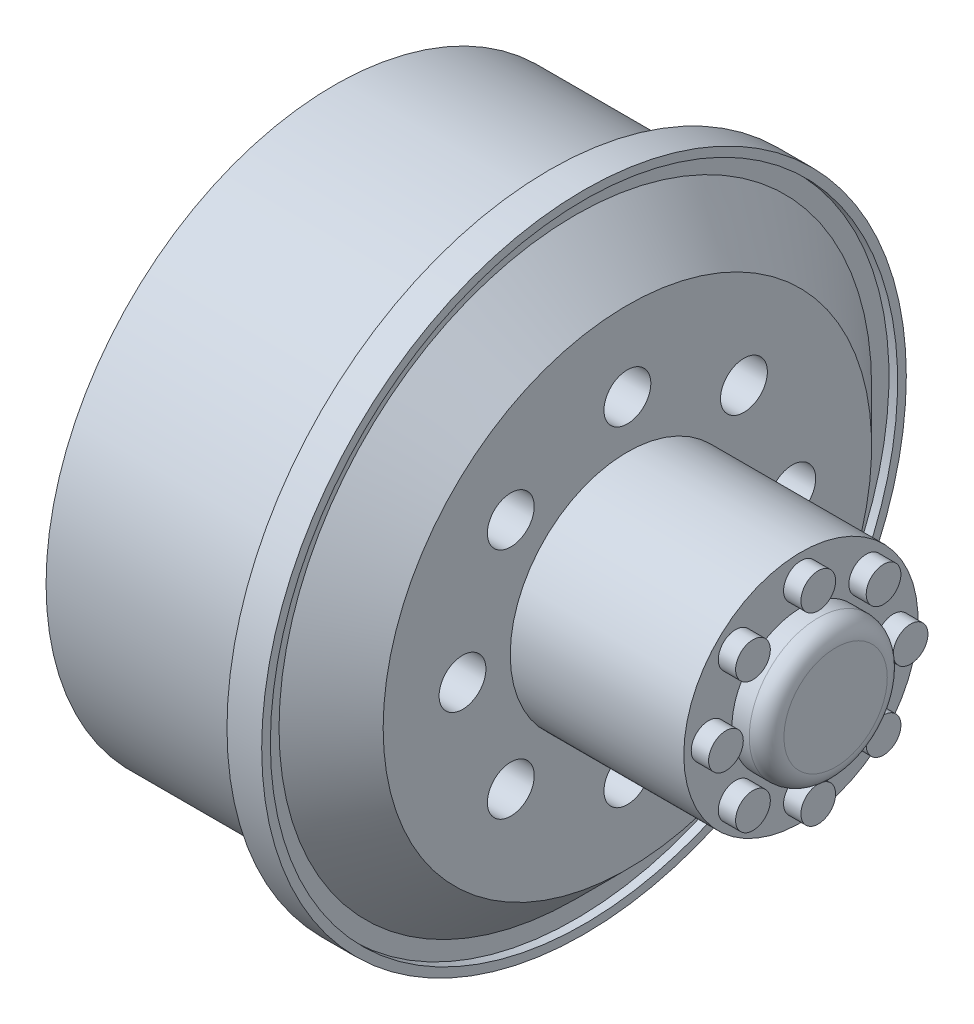
SolidWorks part; units mm, degrees
ref_plane "Front Plane" through (0, 0, 0) normal (0, 0, 1) x (1, 0, 0)
ref_plane "Top Plane" through (0, 0, 0) normal (0, 1, 0) x (1, 0, 0)
ref_plane "Right Plane" through (0, 0, 0) normal (1, 0, 0) x (0, 0, -1)
sketch "Sketch1" plane through (0, 0, 0) normal (0, 0, 1) x (1, 0, 0)
  line L0 (-25, 0) -> (25, 0) construction
  line L1 (0, 58.2583) -> (0, -54.955) construction
  line L2 (-9.3086, 16.6) -> (3.0914, 16.6)
  line L3 (3.0914, 16.6) -> (3.0914, 18.5746)
  line L4 (3.0914, 18.5746) -> (5.0914, 18.5746)
  line L5 (5.0914, 18.5746) -> (5.0914, 18.0746)
  line L6 (5.0914, 18.0746) -> (4.5914, 18.0746)
  line L7 (4.5914, 18.0746) -> (4.5914, 17.0746)
  line L8 (4.5914, 17.0746) -> (7.5914, 14.0746)
  line L9 (7.5914, 14.0746) -> (7.5914, 6.75)
  line L10 (6.5914, 0) -> (5.5914, 0)
  line L11 (-9.3086, 14.6) -> (-9.3086, 16.6)
  line L12 (7.5914, 6.75) -> (17.5914, 6.75)
  line L13 (17.5914, 6.75) -> (17.5914, 0)
  line L14 (-9.3086, 14.6) -> (4.2376, 14.6)
  line L15 (6.5914, 0) -> (17.5914, 0)
  line L16 (4.2376, 14.6) -> (5.5914, 13.2462)
  line L17 (5.5914, 13.2462) -> (5.5914, 0)
  point P20 (7.5914, 10.4123)
  point P23 (6.0914, 15.5746)
  dimension "D1" = 50
  dimension "D2" = 25
  dimension "D3" = 0.5
  dimension "D4" = 2
  dimension "D5" = 1.5
  dimension "D6" = 12.4
  dimension "D7" = 33.2
  dimension "D8" = 2.5
  dimension "D9" = 3
  dimension "D10" = 1
  dimension "D11" = 13.5
  dimension "D12" = 10
  dimension "D13" = 2
  dimension "D14" = 2
  dimension "D15" = 2
revolve "Revolve1" add sketch "Sketch1" angle 360 about L0
sketch "Sketch2" plane through (5.5914, 0, 0) normal (-1, 0, 0) x (0, 0, 1)
  circle A0 centre (0, 0) radius 9.5 construction
  circle A1 centre (0, 9.5) radius 1.35
  circle A2 centre (6.7175, 6.7175) radius 1.35
  circle A3 centre (9.5, 0) radius 1.35
  circle A4 centre (6.7175, -6.7175) radius 1.35
  circle A5 centre (0, -9.5) radius 1.35
  circle A6 centre (-6.7175, -6.7175) radius 1.35
  circle A7 centre (-9.5, 0) radius 1.35
  circle A8 centre (-6.7175, 6.7175) radius 1.35
  point P22 (0, 0)
  dimension "D1" = 19
  dimension "D2" = 2.7
  dimension "D3" = 8
extrude "Cut-Extrude1" cut sketch "Sketch2" against normal blind 10
sketch "Sketch3" plane through (17.5914, 0, 0) normal (1, 0, 0) x (0, 0, -1)
  circle A0 centre (0, 0) radius 3.9771
  circle A1 centre (0, 5.3207) radius 1
  circle A2 centre (3.7623, 3.7623) radius 1
  circle A3 centre (5.3207, 0) radius 1
  circle A4 centre (3.7623, -3.7623) radius 1
  circle A5 centre (0, -5.3207) radius 1
  circle A6 centre (-3.7623, -3.7623) radius 1
  circle A7 centre (-5.3207, 0) radius 1
  circle A8 centre (-3.7623, 3.7623) radius 1
  point P22 (0, 0)
  dimension "D1" = 2
  dimension "D2" = 8
extrude "Boss-Extrude1" add sketch "Sketch3" along normal blind 2
fillet "Fillet1" radius 1 1 edges at (19.5914, 0, -3.9771)
sketch "Sketch4" plane through (19.5914, 0, 0) normal (1, 0, 0) x (0, 0, -1)
  circle A1 centre (0, 5.3207) radius 1
  circle A2 centre (0, 5.3207) radius 1
  circle A3 centre (3.7623, 3.7623) radius 1
  circle A4 centre (3.7623, 3.7623) radius 1
  circle A5 centre (5.3207, 0) radius 1
  circle A6 centre (5.3207, 0) radius 1
  circle A7 centre (3.7623, -3.7623) radius 1
  circle A8 centre (3.7623, -3.7623) radius 1
  circle A9 centre (0, -5.3207) radius 1
  circle A10 centre (0, -5.3207) radius 1
  circle A11 centre (-3.7623, -3.7623) radius 1
  circle A12 centre (-3.7623, -3.7623) radius 1
  circle A13 centre (-5.3207, 0) radius 1
  circle A14 centre (-5.3207, 0) radius 1
  circle A15 centre (-3.7623, 3.7623) radius 1
  circle A16 centre (-3.7623, 3.7623) radius 1
  dimension "D1" = 0
  dimension "D2" = 0
  dimension "D3" = 0
  dimension "D4" = 0
  dimension "D5" = 0
  dimension "D6" = 0
  dimension "D7" = 0
  dimension "D8" = 0
extrude "Cut-Extrude2" cut sketch "Sketch4" against normal blind 1
